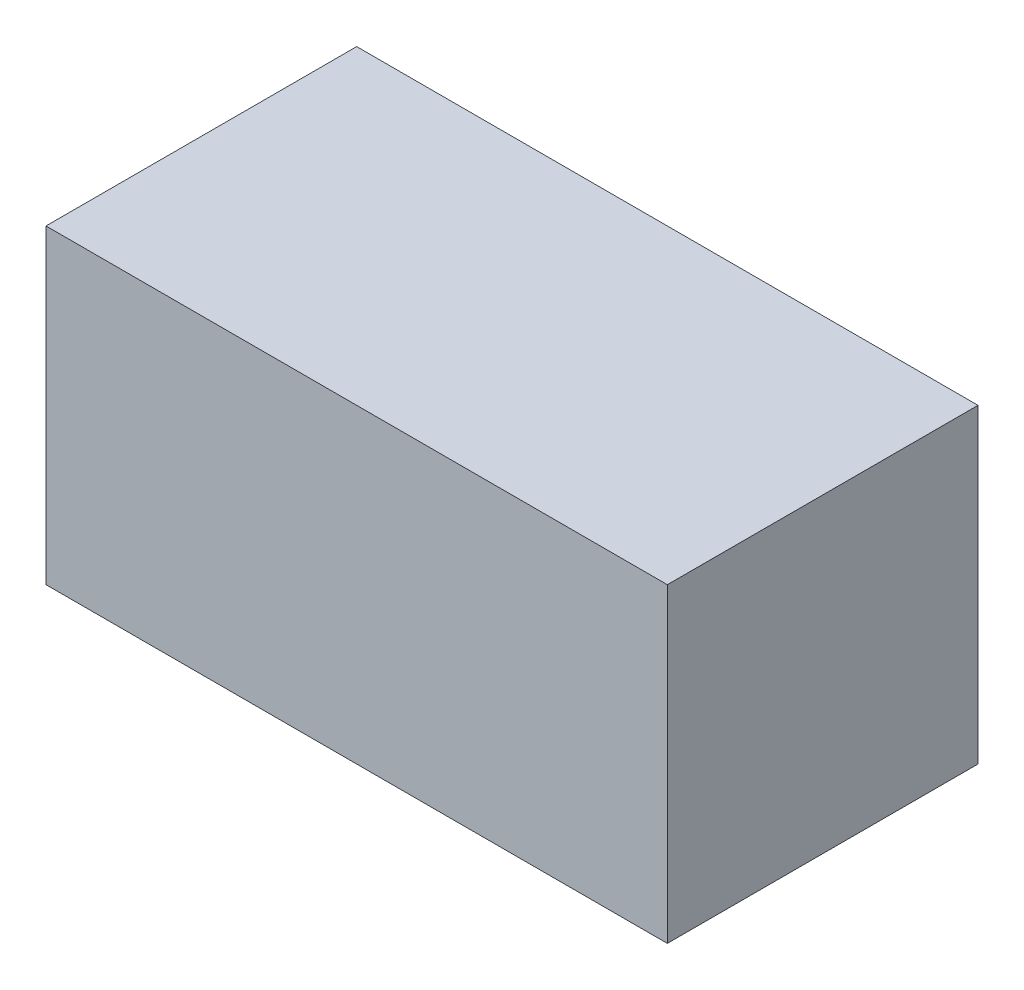
SolidWorks part; units mm, degrees
ref_plane "Front Plane" through (0, 0, 0) normal (0, 0, 1) x (1, 0, 0)
ref_plane "Top Plane" through (0, 0, 0) normal (0, 1, 0) x (1, 0, 0)
ref_plane "Right Plane" through (0, 0, 0) normal (1, 0, 0) x (0, 0, -1)
sketch "Sketch1" plane through (0, 0, 0) normal (0, 1, 0) x (1, 0, 0)
  line L1 (-10, -5) -> (10, -5)
  line L2 (-10, -5) -> (-10, 5)
  line L3 (-10, 5) -> (10, 5)
  line L4 (10, -5) -> (10, 5)
  line L5 (-10, -5) -> (10, 5) construction
  line L6 (-10, 5) -> (10, -5) construction
  point P0 (0, 0)
  dimension "D1" = 20
  dimension "D2" = 10
extrude "Boss-Extrude1" add sketch "Sketch1" along normal mid plane 10
